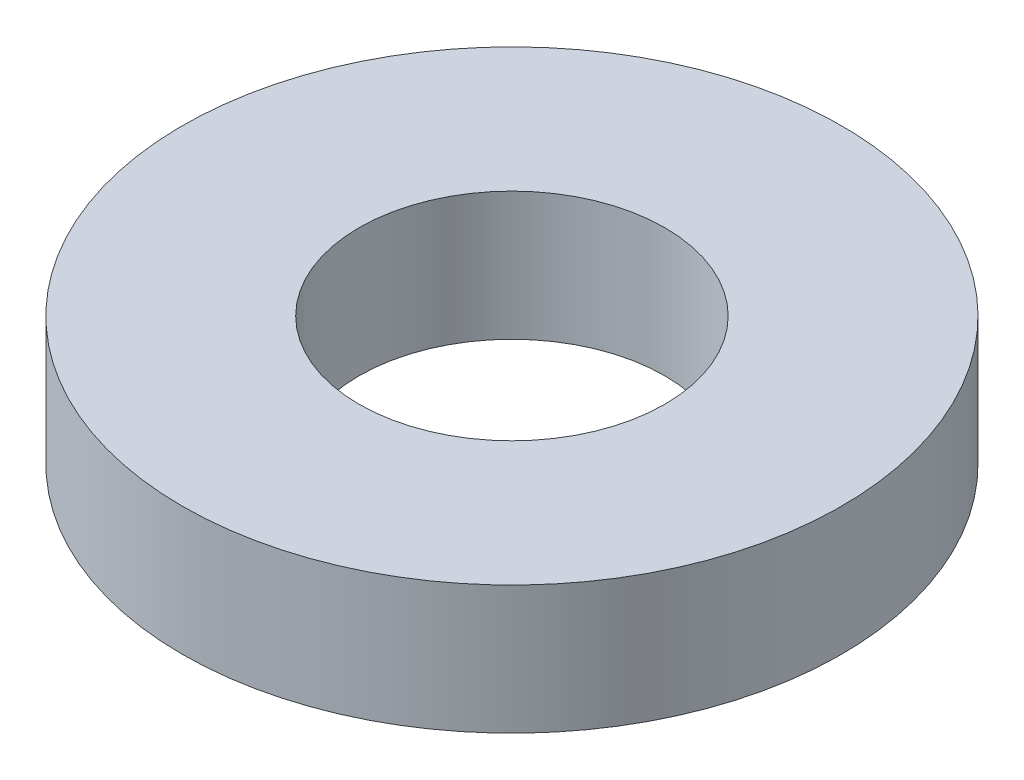
SolidWorks part; units mm, degrees
ref_plane "Front Plane" through (0, 0, 0) normal (0, 0, 1) x (1, 0, 0)
ref_plane "Top Plane" through (0, 0, 0) normal (0, 1, 0) x (1, 0, 0)
ref_plane "Right Plane" through (0, 0, 0) normal (1, 0, 0) x (0, 0, -1)
sketch "Sketch1" plane through (0, 0, 0) normal (0, 1, 0) x (1, 0, 0)
  circle A0 centre (0, 0) radius 4.7625
  dimension "OD" = 9.525
extrude "Boss-Extrude1" add sketch "Sketch1" along normal blind 1.8542
sketch "Sketch5" plane through (0, 1.8542, 0) normal (0, 1, 0) x (-1, 0, 0)
  circle A0 centre (0, 0) radius 2.2098
  dimension "ID" = 4.4196
extrude "Cut-Extrude1" cut sketch "Sketch5" against normal through all
